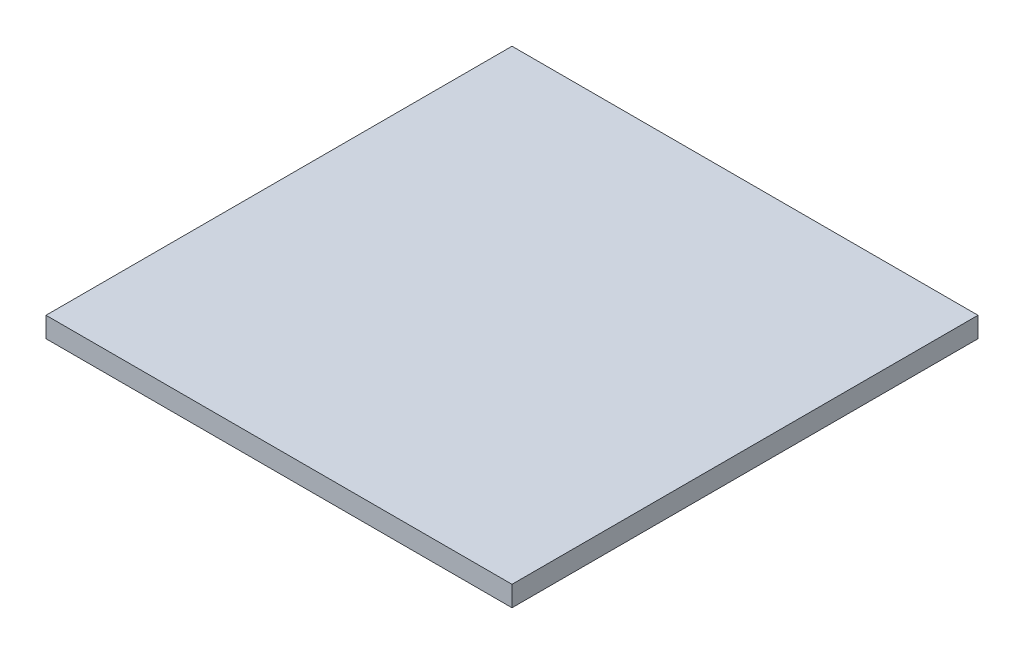
SolidWorks part; units mm, degrees
ref_plane "Front Plane" through (0, 0, 0) normal (0, 0, 1) x (1, 0, 0)
ref_plane "Top Plane" through (0, 0, 0) normal (0, 1, 0) x (1, 0, 0)
ref_plane "Right Plane" through (0, 0, 0) normal (1, 0, 0) x (0, 0, -1)
sketch "Sketch1" plane through (0, 0, 0) normal (0, 1, 0) x (1, 0, 0)
  line L1 (-57.25, -57.25) -> (57.25, -57.25)
  line L2 (-57.25, -57.25) -> (-57.25, 57.25)
  line L3 (-57.25, 57.25) -> (57.25, 57.25)
  line L4 (57.25, -57.25) -> (57.25, 57.25)
  line L5 (-57.25, -57.25) -> (57.25, 57.25) construction
  line L6 (-57.25, 57.25) -> (57.25, -57.25) construction
  point P0 (0, 0)
  dimension "D1" = 114.5
  dimension "D2" = 114.5
extrude "Boss-Extrude1" add sketch "Sketch1" along normal blind 5
